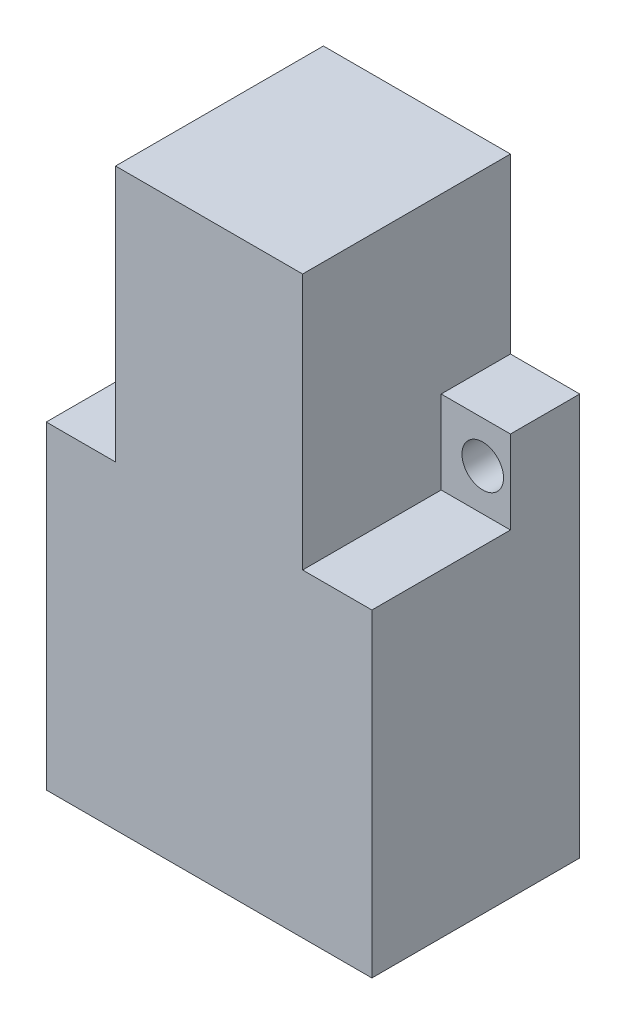
SolidWorks part; units mm, degrees
ref_plane "前视基准面" through (0, 0, 0) normal (0, 0, 1) x (1, 0, 0)
ref_plane "上视基准面" through (0, 0, 0) normal (0, 1, 0) x (1, 0, 0)
ref_plane "右视基准面" through (0, 0, 0) normal (1, 0, 0) x (0, 0, -1)
sketch "草图1" plane through (0, 0, 0) normal (0, 0, 1) x (1, 0, 0)
  line L1 (-11.75, 20.75) -> (11.75, 20.75)
  line L2 (-11.75, 20.75) -> (-11.75, -20.75)
  line L3 (-11.75, -20.75) -> (11.75, -20.75)
  line L4 (11.75, 20.75) -> (11.75, -20.75)
  line L5 (-11.75, 20.75) -> (11.75, -20.75) construction
  line L6 (-11.75, -20.75) -> (11.75, 20.75) construction
  point P0 (0, 0)
  dimension "D1" = 41.5
  dimension "D2" = 23.5
extrude "凸台-拉伸1" add sketch "草图1" along normal blind 15
sketch "草图2" plane through (0, 0, 15) normal (0, 0, 1) x (1, 0, 0)
  line L1 (-11.75, 20.75) -> (-6.75, 20.75)
  line L2 (-11.75, 20.75) -> (-11.75, 2.25)
  line L3 (-11.75, 2.25) -> (-6.75, 2.25)
  line L4 (-6.75, 20.75) -> (-6.75, 2.25)
  line L5 (11.75, 20.75) -> (6.75, 20.75)
  line L6 (11.75, 20.75) -> (11.75, 2.25)
  line L7 (11.75, 2.25) -> (6.75, 2.25)
  line L8 (6.75, 20.75) -> (6.75, 2.25)
  dimension "D1" = 5
  dimension "D2" = 5
  dimension "D3" = 18.5
  dimension "D4" = 18.5
extrude "切除-拉伸1" cut sketch "草图2" against normal blind 10
sketch "草图3" plane through (0, 0, 5) normal (0, 0, 1) x (1, 0, 0)
  line L0 (-6.75, 2.25) -> (-6.75, 20.75) construction
  line L1 (-11.75, 20.75) -> (-6.75, 20.75)
  line L2 (-11.75, 20.75) -> (-11.75, 8.25)
  line L3 (-11.75, 8.25) -> (-6.75, 8.25)
  line L4 (-6.75, 20.75) -> (-6.75, 8.25)
  line L5 (11.75, 2.25) -> (11.75, 20.75) construction
  line L6 (6.75, 20.75) -> (11.75, 20.75)
  line L7 (6.75, 20.75) -> (6.75, 8.25)
  line L8 (6.75, 8.25) -> (11.75, 8.25)
  line L9 (11.75, 20.75) -> (11.75, 8.25)
  dimension "D1" = 12.5
  dimension "D2" = 12.5
extrude "切除-拉伸2" cut sketch "草图3" against normal through all
sketch "草图4" plane through (0, 0, 5) normal (0, 0, 1) x (1, 0, 0)
  line L0 (-11.75, 5.25) -> (11.75, 5.25) construction
  line L1 (-11.75, 8.25) -> (-11.75, 2.25) construction
  line L2 (11.75, 2.25) -> (11.75, 8.25) construction
  line L3 (-9.75, 5.25) -> (9.75, 5.25) construction
  circle A0 centre (-9.75, 5.25) radius 1.5
  circle A1 centre (9.75, 5.25) radius 1.5
  point P9 (0, 5.25)
  dimension "D2" = 3
  dimension "D3" = 3
  dimension "D1" = 19.5
extrude "切除-拉伸3" cut sketch "草图4" against normal through all
